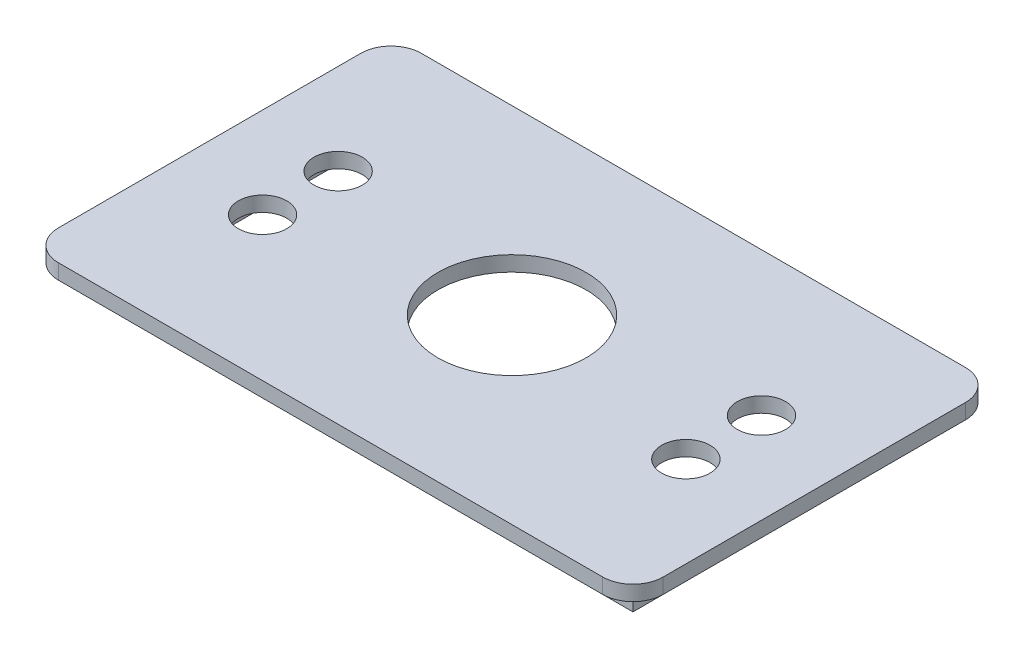
SolidWorks part; units mm, degrees
ref_plane "Front Plane" through (0, 0, 0) normal (0, 0, 1) x (1, 0, 0)
ref_plane "Top Plane" through (0, 0, 0) normal (0, 1, 0) x (1, 0, 0)
ref_plane "Right Plane" through (0, 0, 0) normal (1, 0, 0) x (0, 0, -1)
sketch "Sketch1" plane through (0, 0, 0) normal (0, 1, 0) x (1, 0, 0)
  line L0 (-100, 60) -> (100, -60) construction
  line L1 (-90, 60) -> (90, 60)
  line L2 (-100, 50) -> (-100, -50)
  line L3 (-90, -60) -> (90, -60)
  line L4 (100, 50) -> (100, -50)
  line L5 (-100, -60) -> (100, 60) construction
  line L6 (-70, 12.5) -> (-70, -12.5) construction
  line L7 (70, 12.5) -> (70, -12.5) construction
  circle A0 centre (0, 0) radius 24.5
  circle A1 centre (-70, 12.5) radius 8
  circle A2 centre (-70, -12.5) radius 8
  circle A3 centre (70, 12.5) radius 8
  circle A4 centre (70, -12.5) radius 8
  arc A5 (-100, -50) -> (-90, -60) centre (-90, -50) ccw
  arc A6 (-90, 60) -> (-100, 50) centre (-90, 50) ccw
  arc A7 (90, 60) -> (100, 50) centre (90, 50) cw
  arc A8 (90, -60) -> (100, -50) centre (90, -50) ccw
  point P15 (0, 0)
  point P16 (-70, 0)
  point P17 (70, 0)
  point P18 (0, 0)
  point P19 (60, 0)
  point P20 (-60, -12.5)
  point P21 (-60, -12.5)
  dimension "D2" = 16
  dimension "D3" = 49
  dimension "D9" = 10
  dimension "D1" = 25
  dimension "D4" = 70
  dimension "D5" = 70
  dimension "D6" = 200
  dimension "D7" = 120
  dimension "D8" = 25
extrude "Boss-Extrude1" add sketch "Sketch1" along normal blind 5
sketch "Sketch2" plane through (0, 0, 0) normal (0, -1, 0) x (1, 0, 0)
  line L6 (-90, 50) -> (-90, -50)
  line L7 (-100, -50) -> (-100, 50) construction
  line L8 (-90, 50) -> (90, 50)
  line L9 (-90, -50) -> (90, -50)
  line L10 (90, -50) -> (90, 50)
  line L12 (-90, 60) -> (90, 60) construction
  line L13 (100, 50) -> (100, -50) construction
  line L14 (90, -60) -> (-90, -60) construction
  line L15 (-87, 47) -> (-87, -47)
  line L16 (-87, -47) -> (87, -47)
  line L17 (87, -47) -> (87, 47)
  line L18 (-87, 47) -> (87, 47)
  point P0 (50, 50)
  dimension "D1" = 3
  dimension "D2" = 10
  dimension "D3" = 10
  dimension "D4" = 10
  dimension "D5" = 10
extrude "Boss-Extrude2" add sketch "Sketch2" along normal blind 10
